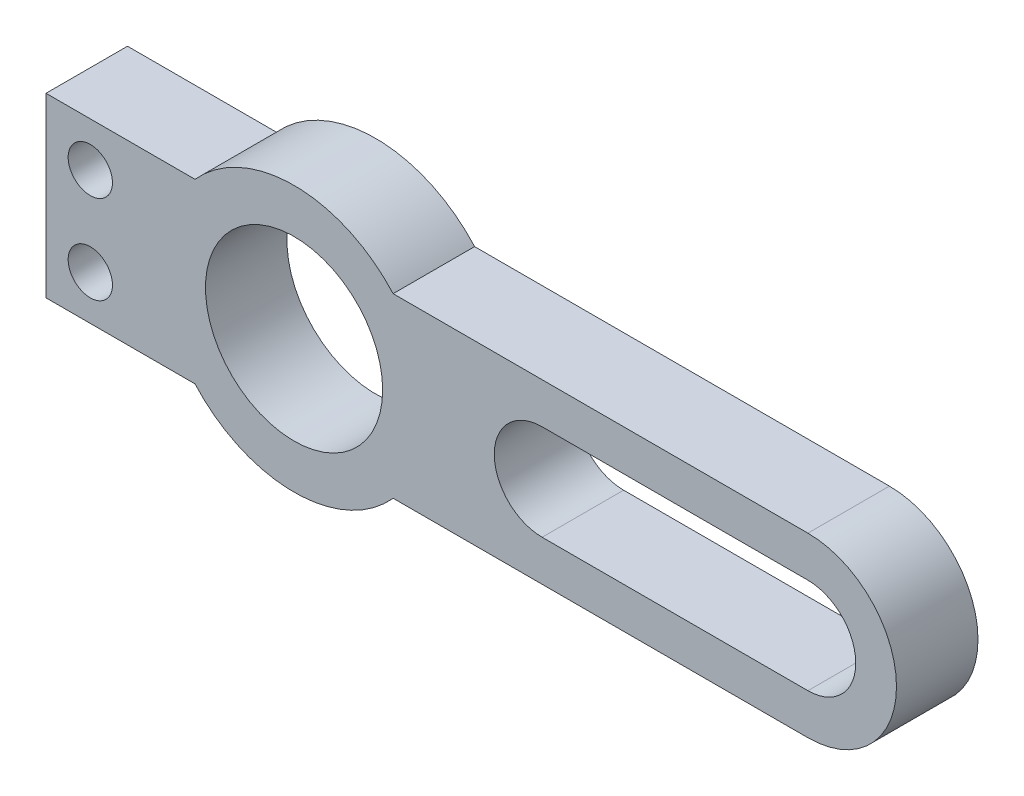
SolidWorks part; units mm, degrees
ref_plane "Front Plane" through (0, 0, 0) normal (0, 0, 1) x (1, 0, 0)
ref_plane "Top Plane" through (0, 0, 0) normal (0, 1, 0) x (1, 0, 0)
ref_plane "Right Plane" through (0, 0, 0) normal (1, 0, 0) x (0, 0, -1)
sketch "Sketch1" plane through (0, 0, 0) normal (0, 0, 1) x (1, 0, 0)
  line L0 (-2.4255, -6.35) -> (27.305, -6.35)
  line L1 (-27.305, -6.35) -> (-16.6245, -6.35)
  line L2 (-27.305, -6.35) -> (-27.305, 6.35)
  line L3 (-27.305, 6.35) -> (-16.6245, 6.35)
  line L4 (27.305, -6.35) -> (27.305, 6.35)
  line L5 (-27.305, -6.35) -> (27.305, 6.35) construction
  line L6 (-27.305, 6.35) -> (27.305, -6.35) construction
  line L7 (-2.4255, 6.35) -> (27.305, 6.35)
  circle A0 centre (-9.525, 0) radius 6.35
  arc A1 (-2.4255, 6.35) -> (-16.6245, 6.35) centre (-9.525, 0) ccw
  arc A2 (-16.6245, -6.35) -> (-2.4255, -6.35) centre (-9.525, 0) ccw
  point P0 (0, 0)
  point P11 (0, 0)
  dimension "D3" = 12.7
  dimension "D4" = 19.05
  dimension "D1" = 12.7
  dimension "D2" = 54.61
  dimension "D5" = 36.83
extrude "Boss-Extrude1" add sketch "Sketch1" along normal blind 6.35
sketch "Sketch2" plane through (0, 0, 6.35) normal (0, 0, 1) x (1, 0, 0)
  line L0 (27.305, -6.35) -> (27.305, 6.35) construction
  circle A0 centre (27.305, 0) radius 6.35
  circle A1 centre (27.305, 0) radius 3.175
  dimension "D1" = 12.7
  dimension "D2" = 3.175
extrude "Boss-Extrude2" add sketch "Sketch2" against normal up to surface (6.35 mm away) up to face at (-4.7625, 0, 0)
sketch "Sketch3" plane through (0, 0, 6.35) normal (0, 0, 1) x (1, 0, 0)
  arc A0 (27.305, -3.175) -> (27.305, 3.175) centre (27.305, 0) ccw construction
  arc A1 (27.305, -3.175) -> (27.305, 3.175) centre (27.305, 0) ccw
  arc A2 (27.305, 3.175) -> (28.7249, -2.8398) centre (27.305, 0) ccw
  line M10 (27.305, -3.175) -> (27.305, 3.175)
extrude "Cut-Extrude1" cut sketch "Sketch3" against normal up to next contours A2 M10
sketch "Sketch4" plane through (0, 0, 6.35) normal (0, 0, 1) x (1, 0, 0)
  line L0 (8.255, 3.175) -> (27.305, 3.175)
  line L1 (8.255, -3.175) -> (27.305, -3.175)
  arc A0 (8.255, 3.175) -> (8.255, -3.175) centre (8.255, 0) ccw
  circle A1 centre (27.305, 0) radius 3.175 construction
  arc A2 (27.305, -3.175) -> (27.305, 3.175) centre (27.305, 0) ccw
  point P9 (10.026, 0)
  point P10 (27.2282, 3.175)
  point P11 (0, 0)
  point P12 (10.5461, 0)
  dimension "D1" = 19.05
extrude "Cut-Extrude2" cut sketch "Sketch4" against normal up to next
sketch "Sketch5" plane through (0, 0, 6.35) normal (0, 0, 1) x (1, 0, 0)
  line L0 (0, 0) -> (-27.305, 0) construction
  line L1 (-27.305, 6.35) -> (-27.305, -6.35) construction
  line L3 (-16.6245, 6.35) -> (-27.305, 6.35) construction
  circle A0 centre (-24.13, 3.175) radius 1.5875
  circle A1 centre (-24.13, -3.175) radius 1.5875
  point P4 (0, 0)
  point P5 (-25.212, 3.5398)
  point P11 (-25.942, 3.4942)
  dimension "D1" = 3.175
  dimension "D2" = 1.5875
  dimension "D3" = 1.5875
extrude "Cut-Extrude3" cut sketch "Sketch5" against normal through all
other "Move Face1" face at (-22.5425, 3.175, 6.35) parameters "D1"=0.508
other "Move Face2" face at (28.8925, 0, 2.921) face at (17.78, 3.175, 2.921) face at (6.6675, 0, 2.921) face at (17.78, -3.175, 2.921) parameters "D1"=0.254
